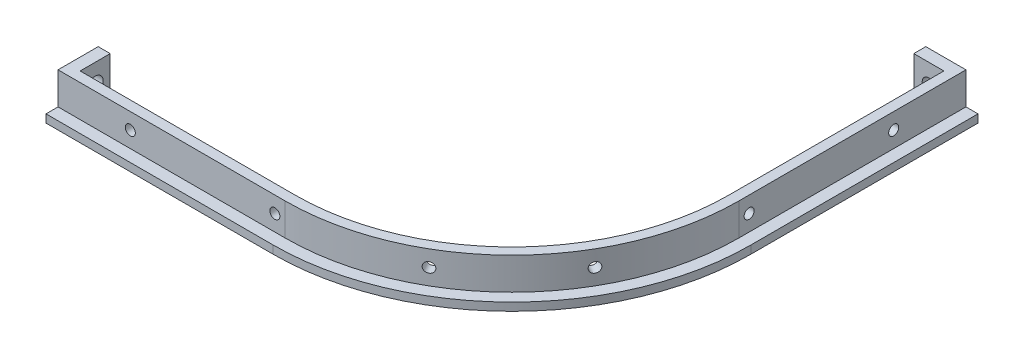
SolidWorks part; units mm, degrees
ref_plane "Front Plane" through (0, 0, 0) normal (0, 0, 1) x (1, 0, 0)
ref_plane "Top Plane" through (0, 0, 0) normal (0, 1, 0) x (1, 0, 0)
ref_plane "Right Plane" through (0, 0, 0) normal (1, 0, 0) x (0, 0, -1)
sketch "Sketch1" plane through (0, 0, 0) normal (0, 1, 0) x (1, 0, 0)
  line L0 (0, 0) -> (0, -145.5772) construction
  line L1 (-56.57, -56.57) -> (56.57, -56.57) construction
  line L2 (-56.57, -56.57) -> (-56.57, 56.57) construction
  line L3 (-56.57, 56.57) -> (56.57, 56.57) construction
  line L4 (56.57, -56.57) -> (56.57, 56.57) construction
  line L5 (-56.57, -56.57) -> (56.57, 56.57) construction
  line L6 (-56.57, 56.57) -> (56.57, -56.57) construction
  line L7 (0, 0) -> (166.7552, 0) construction
  line L8 (0, -116.07) -> (56.57, -116.07)
  line L9 (116.07, -56.57) -> (116.07, 0)
  line L10 (116.07, 0) -> (103.07, 0)
  line L13 (0, -103.07) -> (0, -116.07)
  line L14 (56.57, -110.57) -> (3, -110.57)
  line L15 (3, -110.57) -> (3, -103.07)
  line L16 (3, -103.07) -> (0, -103.07)
  line L17 (110.57, -56.57) -> (110.57, -3)
  line L18 (110.57, -3) -> (103.07, -3)
  line L19 (103.07, -3) -> (103.07, 0)
  circle A0 centre (56.57, -56.57) radius 55 construction
  circle A1 centre (-56.57, -56.57) radius 55 construction
  arc A2 (56.57, -116.07) -> (116.07, -56.57) centre (56.57, -56.57) ccw
  arc A3 (110.57, -56.57) -> (56.57, -110.57) centre (56.57, -56.57) cw
  point P0 (0, 0)
  point P17 (110.57, -2.7707)
  point P20 (0, 0)
  point P27 (105.07, 0)
  dimension "D1" = 110
  dimension "D2" = 113.14
  dimension "D3" = 1
  dimension "D4" = 4.5
  dimension "D5" = 3
  dimension "D6" = 13
extrude "Boss-Extrude1" add sketch "Sketch1" along normal blind 10
sketch "Sketch2" plane through (0, 10, 0) normal (0, 1, 0) x (1, 0, 0)
  circle A0 centre (56.57, -56.57) radius 55.1
  dimension "D1" = 110.2
extrude "Cut-Extrude1" cut sketch "Sketch2" against normal blind 1.1 from offset 1 offset against normal yes
sketch "Sketch3" plane through (0, 10, 0) normal (0, 1, 0) x (1, 0, 0)
  line L2 (116.07, -56.57) -> (116.07, 0) construction
  line L3 (0, -116.07) -> (56.57, -116.07) construction
  line L4 (113.07, -56.57) -> (113.07, 0)
  line L5 (0, -113.07) -> (56.57, -113.07)
  line L6 (113.07, -56.57) -> (113.07, 0)
  line L7 (0, -113.07) -> (56.57, -113.07)
  line L8 (116.07, -56.57) -> (116.07, 0)
  line L9 (0, -116.07) -> (56.57, -116.07)
  line L10 (0, -113.07) -> (0, -116.07)
  line L11 (113.07, 0) -> (116.07, 0)
  arc A1 (56.57, -116.07) -> (116.07, -56.57) centre (56.57, -56.57) ccw construction
  arc A2 (56.57, -113.07) -> (113.07, -56.57) centre (56.57, -56.57) ccw
  arc A3 (56.57, -113.07) -> (113.07, -56.57) centre (56.57, -56.57) ccw
  arc A4 (56.57, -116.07) -> (116.07, -56.57) centre (56.57, -56.57) ccw
  dimension "D1" = 3
extrude "Cut-Extrude2" cut sketch "Sketch3" against normal blind 8
sketch "Sketch4" plane through (3, 0, 0) normal (1, 0, 0) x (0, 0, -1)
  line L0 (-106.82, 10) -> (-106.82, 0) construction
  line L1 (-110.57, 10) -> (-103.07, 10) construction
  line L2 (-110.57, 0) -> (-103.07, 0) construction
  circle A0 centre (-106.82, 5) radius 2
  point P8 (-107.07, 5)
  dimension "D1" = 4
extrude "Cut-Extrude3" cut sketch "Sketch4" against normal through all
sketch "Sketch5" plane through (0, 0, 3) normal (0, 0, 1) x (1, 0, 0)
  line L0 (106.82, 10) -> (106.82, 0) construction
  line L1 (103.07, 10) -> (110.57, 10) construction
  line L2 (103.07, 0) -> (110.57, 0) construction
  circle A0 centre (106.82, 5) radius 1.65
  dimension "D1" = 3.3
extrude "Cut-Extrude4" cut sketch "Sketch5" against normal through all
sketch "Sketch6" plane through (0, 0, 0) normal (0, 1, 0) x (1, 0, 0)
  line L0 (0, 0) -> (116.2359, -116.2359) construction
  line L1 (0, 0) -> (0, -36.3227) construction
  line L2 (0, 0) -> (-18.742, -18.742) construction
  dimension "D1" = 45
ref_plane "Plane1" through (0, 0, 0) normal (-0.7071, 0, 0.7071) x (0.7071, 0, 0.7071)
sketch "Sketch7" plane through (0, 0, 113.07) normal (0, 0, 1) x (1, 0, 0)
  line L0 (0, 2) -> (0, 10) construction
  line L1 (-1.0934, 6) -> (63.135, 6) construction
  line L2 (56.57, 2) -> (0, 2) construction
  line L3 (56.57, 10) -> (0, 10) construction
  circle A0 centre (18, 6) radius 1.25
  circle A1 centre (54, 6) radius 1.25
  point P12 (0, 0)
  point P13 (18, 6)
  point P14 (54, 6)
  dimension "D3" = 2.5
  dimension "D1" = 54
  dimension "D2" = 18
extrude "Cut-Extrude5" cut sketch "Sketch7" against normal through all
sketch "Sketch8" plane through (0, 0, 0) normal (0, 1, 0) x (1, 0, 0)
  line L0 (49.368, -125.9687) -> (120.272, -85.0322) construction
  line L1 (0, 0) -> (0, -36.3227) construction
  line L2 (84.82, -105.5004) -> (79.4037, -96.1191) construction
  arc A0 (56.57, -113.07) -> (113.07, -56.57) centre (56.57, -56.57) ccw construction
  point P9 (84.82, -105.5004)
  point P10 (85.7916, -104.9395)
  point P11 (83.8151, -106.0806)
  dimension "D1" = 60
ref_plane "Plane2" through (66.888, 0, 115.8535) normal (-0.5, 0, -0.866) x (-0.866, 0, 0.5)
sketch "Sketch9" plane through (66.888, 0, 115.8535) normal (-0.5, 0, -0.866) x (-0.866, 0, 0.5)
  line L0 (-13.2533, 6) -> (-27.2877, 6) construction
  line L1 (7.5439, 10) -> (-69.6365, 10) construction
  line L2 (7.5439, 2) -> (-69.6365, 2) construction
  line L3 (-20.7061, 0) -> (-20.7061, 6) construction
  circle A0 centre (-20.7061, 6) radius 1.25
  point P8 (-21.0523, 6)
  dimension "D1" = 2.5
extrude "Cut-Extrude6" cut sketch "Sketch9" along normal through all
mirror "Mirror1" about plane through (0, 0, 0) normal (-0.7071, 0, 0.7071) of "Cut-Extrude5", "Cut-Extrude6"
